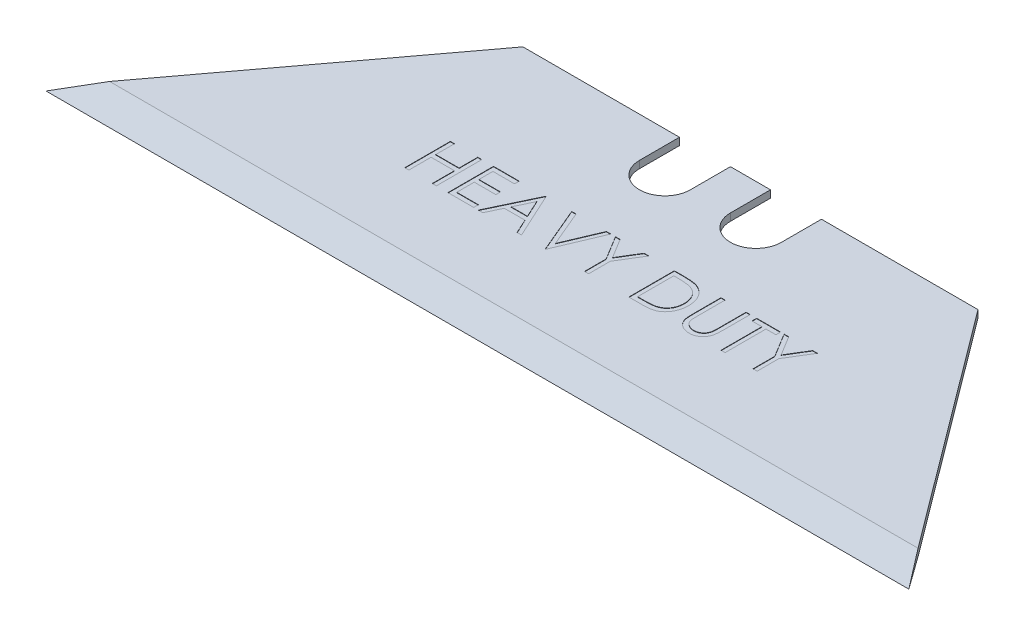
SolidWorks part; units mm, degrees
material "Alloy Steel"
ref_plane "Front" through (0, 0, 0) normal (0, 0, 1) x (1, 0, 0)
ref_plane "Top" through (0, 0, 0) normal (0, 1, 0) x (1, 0, 0)
ref_plane "Right" through (0, 0, 0) normal (1, 0, 0) x (0, 0, -1)
sketch "Sketch1" plane through (0, 0, 0) normal (0, 1, 0) x (1, 0, 0)
  line L0 (-15.875, 6.578) -> (-30.099, -12.472)
  line L1 (30.099, -12.472) -> (-30.099, -12.472)
  line L3 (15.875, 6.578) -> (-15.875, 6.578)
  line L5 (30.099, -12.472) -> (-15.875, 6.578) construction
  line L6 (15.875, 6.578) -> (-30.099, -12.472) construction
  line L7 (15.875, 6.578) -> (30.099, -12.472)
  point P0 (0, 0)
  dimension "D1" = 60.198
  dimension "D2" = 19.05
  dimension "D3" = 31.75
extrude "Boss-Extrude1" add sketch "Sketch1" along normal mid plane 0.508
sketch "Sketch2" plane through (0, 0.254, 0) normal (0, 1, 0) x (1, 0, 0)
  line L1 (-30.099, -12.472) -> (30.099, -12.472) construction
  line L2 (-4.953, 3.784) -> (-4.953, 6.578)
  line L3 (15.875, 6.578) -> (-15.875, 6.578) construction
  line L4 (-4.953, 6.578) -> (-1.397, 6.578)
  line L5 (-1.397, 6.578) -> (-1.397, 3.784)
  line L6 (1.397, 3.784) -> (1.397, 6.578)
  line L7 (1.397, 6.578) -> (4.953, 6.578)
  line L8 (4.953, 6.578) -> (4.953, 3.784)
  arc A0 (-4.953, 3.784) -> (-1.397, 3.784) centre (-3.175, 3.784) ccw
  arc A1 (1.397, 3.784) -> (4.953, 3.784) centre (3.175, 3.784) ccw
  point P4 (1.397, 3.784)
  point P5 (-3.175, 2.006)
  point P8 (-4.953, 3.784)
  point P9 (4.953, 3.784)
  point P10 (15.875, 6.578)
  point P17 (-1.397, 3.784)
  dimension "D1" = 3.556
  dimension "D3" = 2.794
  dimension "D2" = 14.478
  dimension "D4" = 10.922
extrude "Cut-Extrude1" cut sketch "Sketch2" against normal through all
sketch "Sketch3" plane through (0, 0, 0) normal (1, 0, 0) x (0, 0, -1)
  line L0 (-12.472, 0) -> (-9.932, 0.254)
  line L1 (-12.472, 0.254) -> (-12.472, -0.254) construction
  line L2 (-12.472, 0.254) -> (6.578, 0.254) construction
  line L3 (-9.932, 0.254) -> (-12.472, 0.254)
  line L4 (-12.472, 0.254) -> (-12.472, 0)
  dimension "D1" = 2.54
extrude "Cut-Extrude2" cut sketch "Sketch3" along normal through all both and the other way through all
mirror "Mirror1" about plane through (0, 0, 0) normal (0, 1, 0) of "Cut-Extrude2"
sketch "Sketch4" plane through (0, 0.254, 0) normal (0, 1, 0) x (1, 0, 0)
  text T0 "HEAVY DUTY"
extrude "Cut-Extrude3" cut sketch "Sketch4" against normal blind 0.0254
